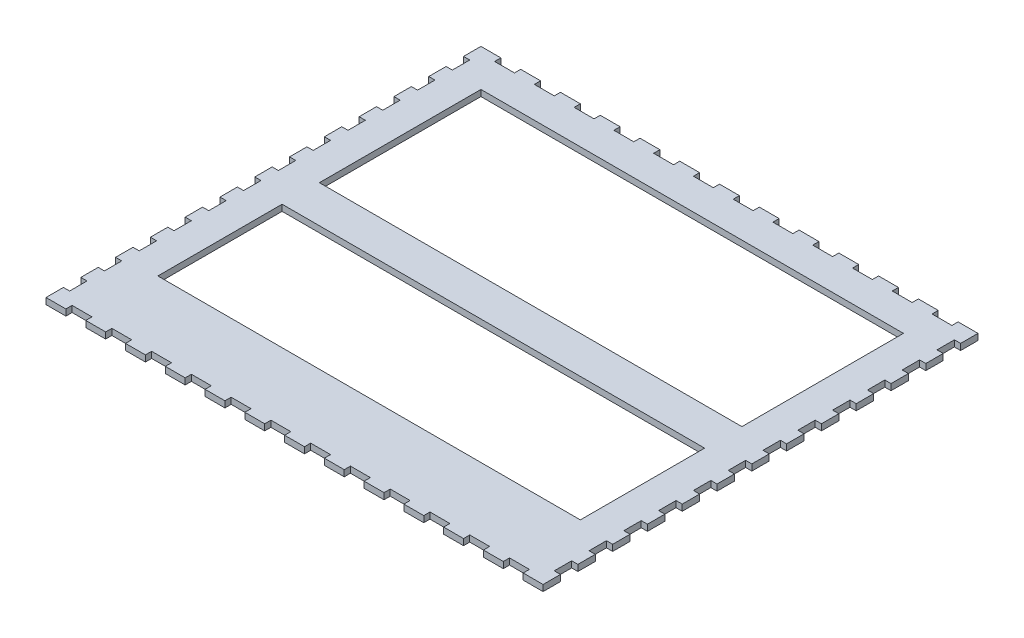
SolidWorks part; units mm, degrees
ref_plane "Plan de face" through (0, 0, 0) normal (0, 0, 1) x (1, 0, 0)
ref_plane "Plan de dessus" through (0, 0, 0) normal (0, 1, 0) x (1, 0, 0)
ref_plane "Plan de droite" through (0, 0, 0) normal (1, 0, 0) x (0, 0, -1)
sketch "Esquisse1" plane through (0, 0, 0) normal (0, 1, 0) x (1, 0, 0)
  line L1 (0, 0) -> (400, 0)
  line L2 (0, 0) -> (0, -350)
  line L3 (0, -350) -> (400, -350)
  line L4 (400, 0) -> (400, -350)
  dimension "D1" = 400
  dimension "D2" = 350
extrude "Boss.-Extru.1" add sketch "Esquisse1" along normal blind 5
ref_plane "Plan2" through (0, 0, 175) normal (0, 0, -1) x (-1, 0, 0)
ref_plane "Plan3" through (200, 0, 0) normal (1, 0, 0) x (0, 0, -1)
sketch "Esquisse2" plane through (0, 5, 0) normal (0, 1, 0) x (1, 0, 0)
  line L0 (400, 0) -> (0, 0) construction
  line L1 (16, 0) -> (32, 0)
  line L2 (16, 0) -> (16, -5)
  line L3 (16, -5) -> (32, -5)
  line L4 (32, 0) -> (32, -5)
  line L7 (0, 0) -> (400, 0) construction
  line L8 (0, 0) -> (0, -350) construction
  dimension "D1" = 400
  dimension "D2" = 16
  dimension "D3" = 16
  dimension "D4" = 5
extrude "Enlèv. mat.-Extru.1" cut sketch "Esquisse2" against normal blind 5
pattern_linear "Répétition linéaire1" count 12 spacing 32 along (1, 0, 0) of "Enlèv. mat.-Extru.1"
sketch "Esquisse3" plane through (0, 5, 0) normal (0, 1, 0) x (1, 0, 0)
  line L0 (0, 0) -> (0, -350) construction
  line L1 (0, -14) -> (5, -14)
  line L2 (0, -14) -> (0, -28)
  line L3 (0, -28) -> (5, -28)
  line L4 (5, -14) -> (5, -28)
  line L5 (0, 0) -> (0, -350) construction
  line L6 (0, -350) -> (400, -350) construction
  line L7 (16, 0) -> (0, 0) construction
  dimension "D4" = 5
  dimension "D1" = 350
  dimension "D2" = 14
  dimension "D3" = 14
extrude "Enlèv. mat.-Extru.2" cut sketch "Esquisse3" against normal blind 5
pattern_linear "Répétition linéaire2" count 12 spacing 28 along (0, 0, 1) of "Enlèv. mat.-Extru.2"
mirror "Symétrie1" about plane through (0, 0, 175) normal (0, 0, -1) of "Répétition linéaire1", "Enlèv. mat.-Extru.1"
mirror "Symétrie2" about plane through (200, 0, 0) normal (1, 0, 0) of "Répétition linéaire2", "Enlèv. mat.-Extru.2"
sketch "Esquisse4" plane through (0, 5, 0) normal (0, 1, 0) x (1, 0, 0)
  line L0 (200, -2.75) -> (200, 2.75) construction
  line L1 (30, -30) -> (370, -30)
  line L2 (30, -30) -> (30, -160)
  line L3 (30, -160) -> (370, -160)
  line L4 (370, -30) -> (370, -160)
  line L5 (2.75, -175) -> (-2.75, -175) construction
  dimension "D1" = 340
  dimension "D2" = 170
  dimension "D3" = 130
  dimension "D4" = 15
extrude "Enlèv. mat.-Extru.3" cut sketch "Esquisse4" against normal blind 10
sketch "Esquisse5" plane through (0, 5, 0) normal (0, 1, 0) x (1, 0, 0)
  line L0 (30, -30) -> (30, -160) construction
  line L1 (30, -190) -> (370, -190)
  line L2 (30, -190) -> (30, -290)
  line L3 (30, -290) -> (370, -290)
  line L4 (370, -190) -> (370, -290)
  line L5 (370, -160) -> (370, -30) construction
  line L7 (2.75, -175) -> (-2.75, -175) construction
  dimension "D1" = 15
  dimension "D2" = 100
extrude "Enlèv. mat.-Extru.4" cut sketch "Esquisse5" against normal blind 10
equation "\"D2@Esquisse2\"=\"D1@Esquisse2\"/25"
equation "\"D3@Esquisse2\"=\"D2@Esquisse2\""
equation "\"D4@Répétition linéaire1\"=\"D2@Esquisse2\"*2"
equation "\"D3@Répétition linéaire1\"=\"D2@Esquisse2\"*2"
equation "\"D2@Esquisse3\"=\"D1@Esquisse3\"/25"
equation "\"D3@Esquisse3\"=\"D2@Esquisse3\""
equation "\"D3@Répétition linéaire2\"=\"D2@Esquisse3\"*2"
equation "\"D2@Esquisse4\"=\"D1@Esquisse4\"/2"
